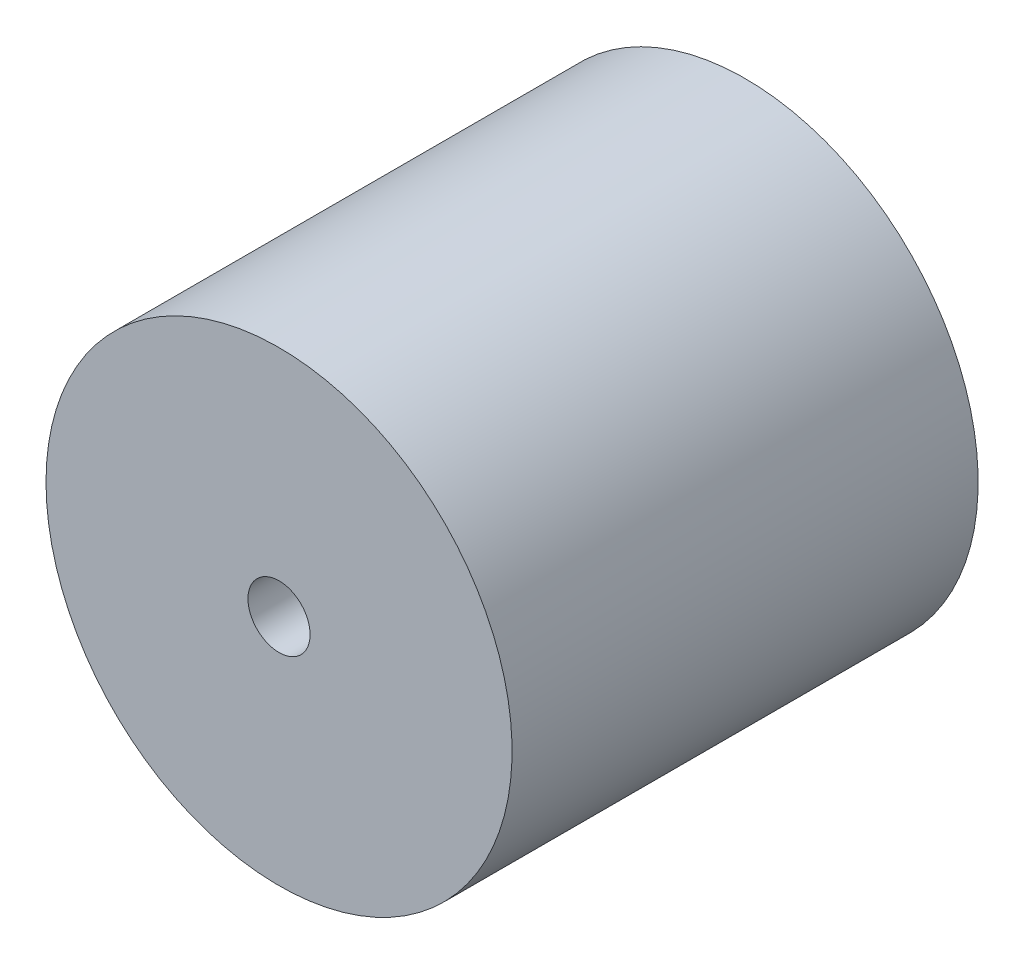
SolidWorks part; units mm, degrees
ref_plane "Plan de face" through (0, 0, 0) normal (0, 0, 1) x (1, 0, 0)
ref_plane "Plan de dessus" through (0, 0, 0) normal (0, 1, 0) x (1, 0, 0)
ref_plane "Plan de droite" through (0, 0, 0) normal (1, 0, 0) x (0, 0, -1)
ref_plane "Plan1" through (0, 0, 0) normal (0, -1, 0) x (1, 0, 0)
sketch "Esquisse1" plane through (0, 0, 0) normal (0, -1, 0) x (1, 0, 0)
  line L0 (7.5, 15) -> (1, 15)
  line L1 (1, 15) -> (1, 0)
  line L2 (1, 0) -> (7.5, 0)
  line L3 (7.5, 0) -> (7.5, 15)
  line L4 (0, 15) -> (0, 0) construction
revolve "Révolution1" add sketch "Esquisse1" angle 360 about L4
